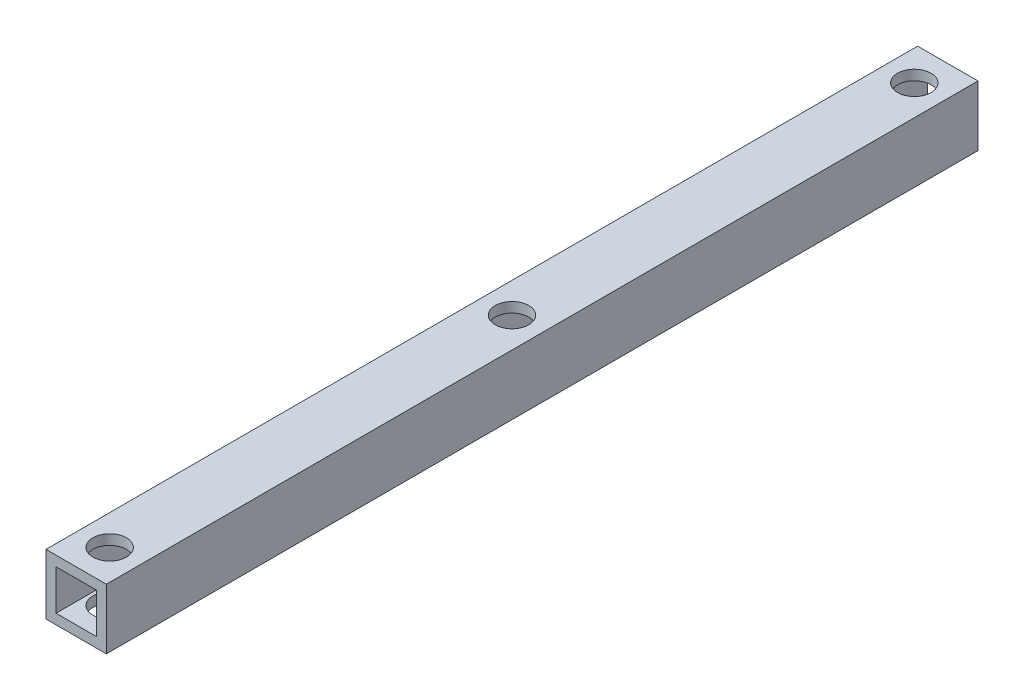
SolidWorks part; units mm, degrees
ref_plane "正面" through (0, 0, 0) normal (0, 0, 1) x (1, 0, 0)
ref_plane "平面" through (0, 0, 0) normal (0, 1, 0) x (1, 0, 0)
ref_plane "右側面" through (0, 0, 0) normal (1, 0, 0) x (0, 0, -1)
sketch "ｽｹｯﾁ1" plane through (0, 0, 0) normal (0, 0, 1) x (1, 0, 0)
  line L1 (-4.5, 4.5) -> (4.5, 4.5)
  line L2 (-4.5, 4.5) -> (-4.5, -4.5)
  line L3 (-4.5, -4.5) -> (4.5, -4.5)
  line L4 (4.5, 4.5) -> (4.5, -4.5)
  line L5 (-4.5, 4.5) -> (4.5, -4.5) construction
  line L6 (-4.5, -4.5) -> (4.5, 4.5) construction
  line L7 (-3, 3) -> (3, 3)
  line L8 (-3, 3) -> (-3, -3)
  line L9 (-3, -3) -> (3, -3)
  line L10 (3, 3) -> (3, -3)
  line L11 (-3, 3) -> (3, -3) construction
  line L12 (-3, -3) -> (3, 3) construction
  point P0 (0, 0)
  point P6 (0, 0)
  dimension "D1" = 9
  dimension "D2" = 9
  dimension "D3" = 6
  dimension "D4" = 6
extrude "ﾎﾞｽ - 押し出し1" add sketch "ｽｹｯﾁ1" along normal blind 130
sketch "ｽｹｯﾁ2" plane through (0, 4.5, 0) normal (0, 1, 0) x (1, 0, 0)
  line L0 (0, 0) -> (0, -5)
  line L1 (0, -130) -> (0, -125)
  line L2 (4.5, -130) -> (-4.5, -130) construction
  line L3 (0, -65) -> (0, 0)
  circle A0 centre (0, -65) radius 2.5
  circle A1 centre (0, -5) radius 2.5
  circle A2 centre (0, -125) radius 2.5
  dimension "D3" = 5
  dimension "D4" = 5
  dimension "D5" = 5
  dimension "D1" = 5
  dimension "D2" = 5
  dimension "D6" = 65
extrude "ｶｯﾄ - 押し出し1" cut sketch "ｽｹｯﾁ2" against normal blind 90
